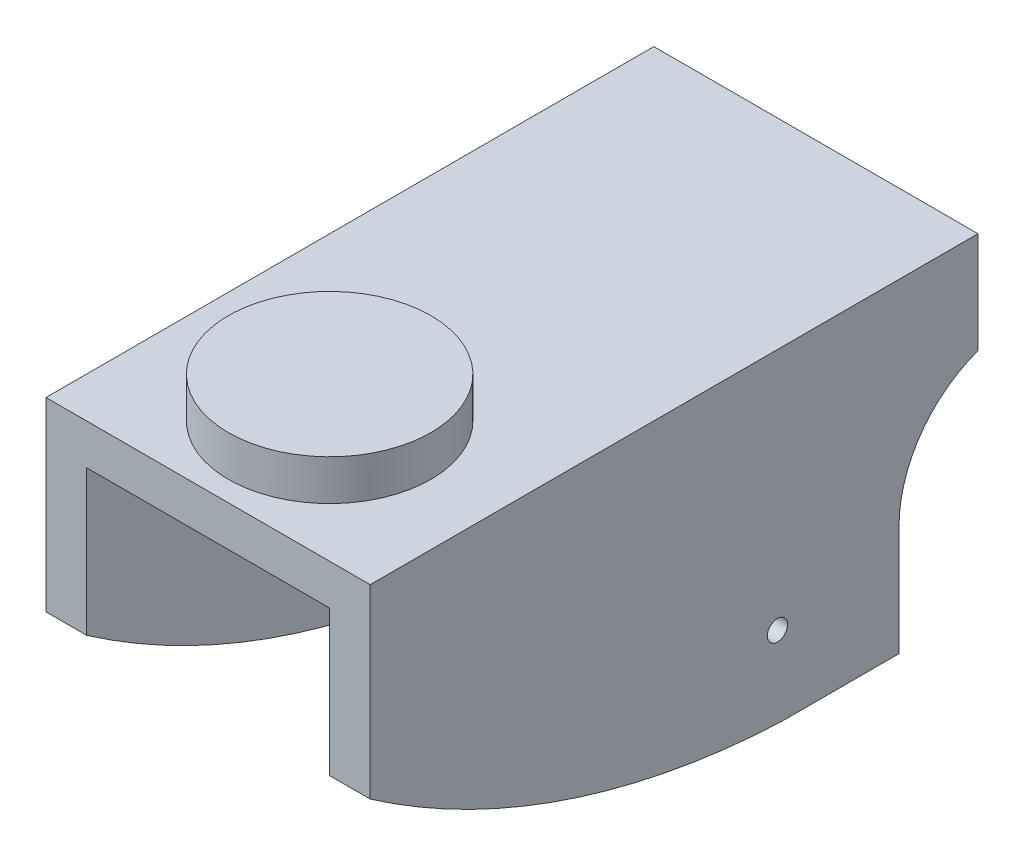
SolidWorks part; units mm, degrees
ref_plane "Front Plane" through (0, 0, 0) normal (0, 0, 1) x (1, 0, 0)
ref_plane "Top Plane" through (0, 0, 0) normal (0, 1, 0) x (1, 0, 0)
ref_plane "Right Plane" through (0, 0, 0) normal (1, 0, 0) x (0, 0, -1)
sketch "Sketch2" plane through (0, 0, 0) normal (1, 0, 0) x (0, 0, -1)
  line L0 (0, 0) -> (38.1, 0)
  line L1 (38.1, 0) -> (38.1, -6.35)
  line L4 (33.1497, -20.32) -> (25.7531, -20.32)
  line L7 (0, -11.6377) -> (0, 0)
  line L8 (33.1497, -20.32) -> (33.1497, -13.4044)
  arc A0 (0, -11.6377) -> (25.7531, -20.32) centre (27.8343, 28.3885) ccw
  arc A1 (38.1, -6.35) -> (33.1497, -13.4044) centre (40.622, -13.3839) ccw
  point P10 (0, 0)
  point P11 (39.4997, -13.3839)
  point P12 (25.7531, -20.32)
  dimension "D1" = 38.1
  dimension "D2" = 6.35
  dimension "D3" = 20.32
extrude "Boss-Extrude1" add sketch "Sketch2" along normal blind 20.32
shell "Shell1" thickness 2.54
sketch "Sketch3" plane through (0, 0, 0) normal (0, 1, 0) x (1, 0, 0)
  line L0 (0, 38.1) -> (0, 0) construction
  line L1 (20.32, 0) -> (0, 0) construction
  circle A0 centre (10.16, 7.62) radius 6.35
  point P6 (10.16, 0)
  dimension "D1" = 12.7
  dimension "D2" = 10.16
  dimension "D3" = 7.62
extrude "Boss-Extrude2" add sketch "Sketch3" along normal blind 2.54
sketch "Sketch5" plane through (20.32, 0, 0) normal (1, 0, 0) x (0, 0, -1)
  line L0 (25.7531, -20.32) -> (33.1497, -20.32) construction
  line L2 (33.1497, -20.32) -> (33.1497, -13.4044) construction
  circle A0 centre (25.5297, -15.24) radius 0.635
  point P4 (0, 0)
  point P6 (39.4997, -14.772)
  dimension "D3" = 1.27
  dimension "D1" = 5.08
  dimension "D2" = 7.62
extrude "Cut-Extrude2" cut sketch "Sketch5" against normal through all both and the other way through all
